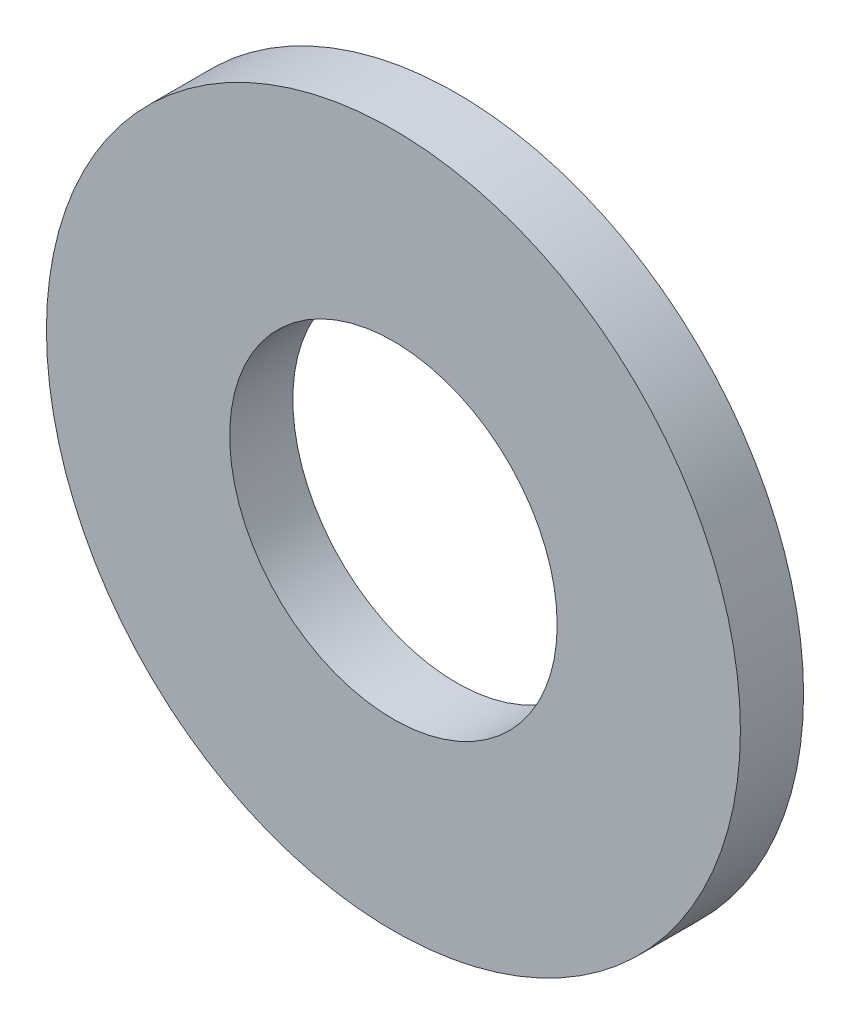
SolidWorks part; units mm, degrees
ref_plane "Front Plane" through (0, 0, 0) normal (0, 0, 1) x (1, 0, 0)
ref_plane "Top Plane" through (0, 0, 0) normal (0, 1, 0) x (1, 0, 0)
ref_plane "Right Plane" through (0, 0, 0) normal (1, 0, 0) x (0, 0, -1)
sketch "Sketch1" plane through (0, 0, 0) normal (0, 0, 1) x (1, 0, 0)
  circle A0 centre (0, 0) radius 2.1
  circle A1 centre (0, 0) radius 4.45
  dimension "D1" = 8.9
  dimension "D2" = 4.2
extrude "Boss-Extrude1" add sketch "Sketch1" along normal blind 0.81
